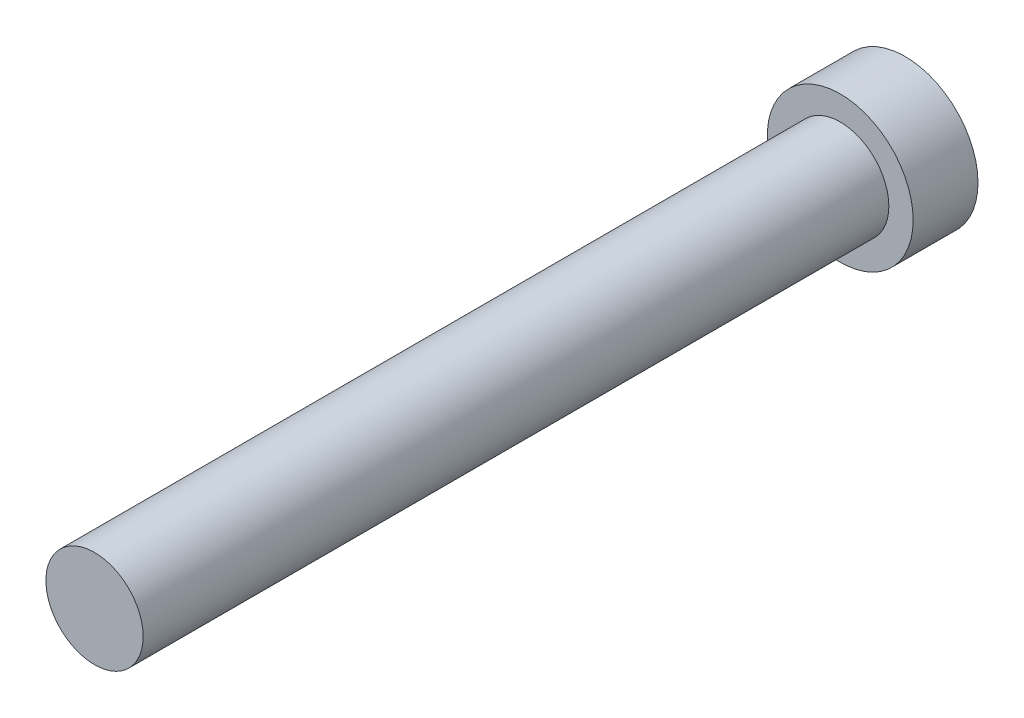
SolidWorks part; units mm, degrees
ref_plane "Front Plane" through (0, 0, 0) normal (0, 0, 1) x (1, 0, 0)
ref_plane "Top Plane" through (0, 0, 0) normal (0, 1, 0) x (1, 0, 0)
ref_plane "Right Plane" through (0, 0, 0) normal (1, 0, 0) x (0, 0, -1)
sketch "Sketch1" plane through (0, 0, 0) normal (0, 0, 1) x (1, 0, 0)
  circle A0 centre (0, 0) radius 22.5
  dimension "D1" = 45
extrude "Boss-Extrude1" add sketch "Sketch1" along normal blind 20
sketch "Sketch2" plane through (0, 0, 20) normal (0, 0, 1) x (1, 0, 0)
  circle A0 centre (0, 0) radius 15
  dimension "D1" = 30
extrude "Boss-Extrude2" add sketch "Sketch2" along normal blind 230
